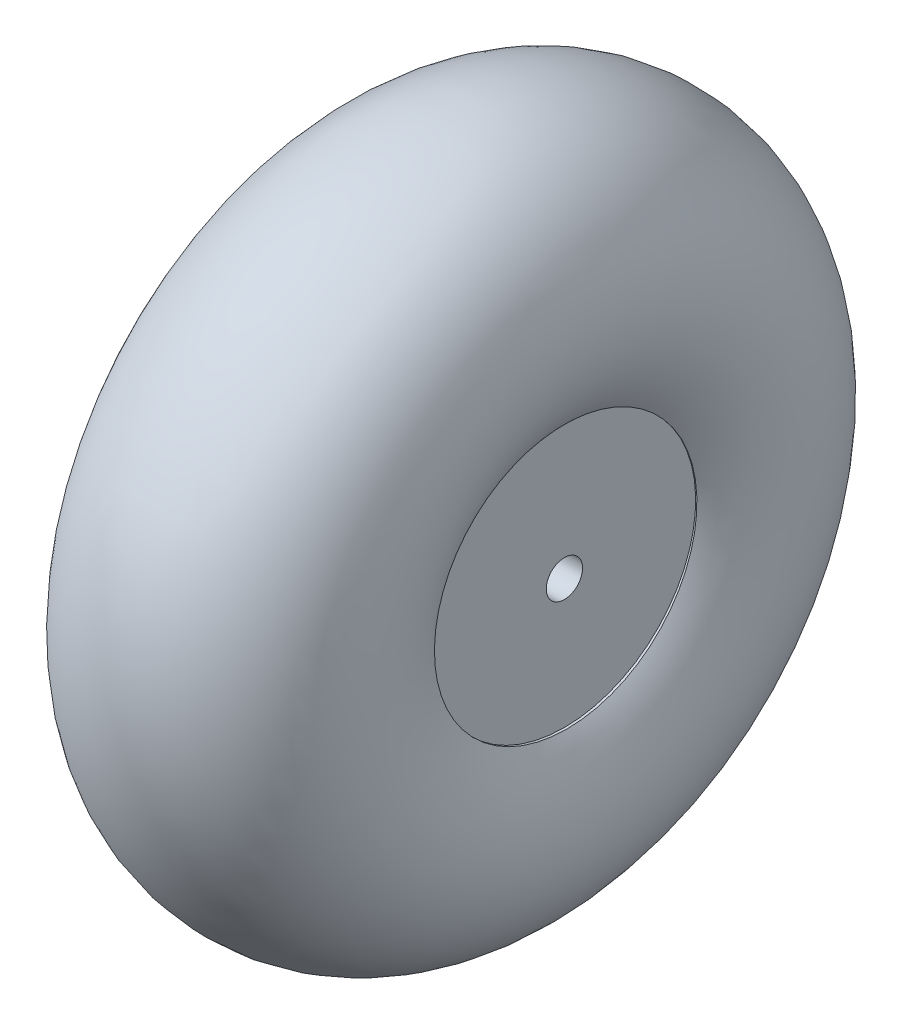
SolidWorks part; units mm, degrees
ref_plane "Front Plane" through (0, 0, 0) normal (0, 0, 1) x (1, 0, 0)
ref_plane "Top Plane" through (0, 0, 0) normal (0, 1, 0) x (1, 0, 0)
ref_plane "Right Plane" through (0, 0, 0) normal (1, 0, 0) x (0, 0, -1)
sketch "Sketch1" plane through (0, 0, 0) normal (0, 0, 1) x (1, 0, 0)
  line L0 (0, 0) -> (21.5286, 0) construction
  line L2 (0, 1) -> (12.7, 1)
  line L3 (0, 1) -> (0, 7.35)
  line L4 (0, 7.35) -> (12.7, 7.35)
  line L5 (12.7, 1) -> (12.7, 7.35)
  dimension "D1" = 6.35
  dimension "D2" = 12.7
  dimension "D3" = 1
revolve "Revolve1" add sketch "Sketch1" angle 360 about L0
sketch "Sketch2" plane through (0, 0, 0) normal (0, 0, 1) x (1, 0, 0)
  line L0 (0, 0) -> (39.5869, 0.3853) construction
  line L1 (0, 7.35) -> (12.7, 7.35)
  arc A0 (0, 7.35) -> (12.7, 7.35) centre (6.35, 11.5621) cw
  dimension "D1" = 7.62
revolve "Revolve8" add sketch "Sketch2" angle 360 about L0
